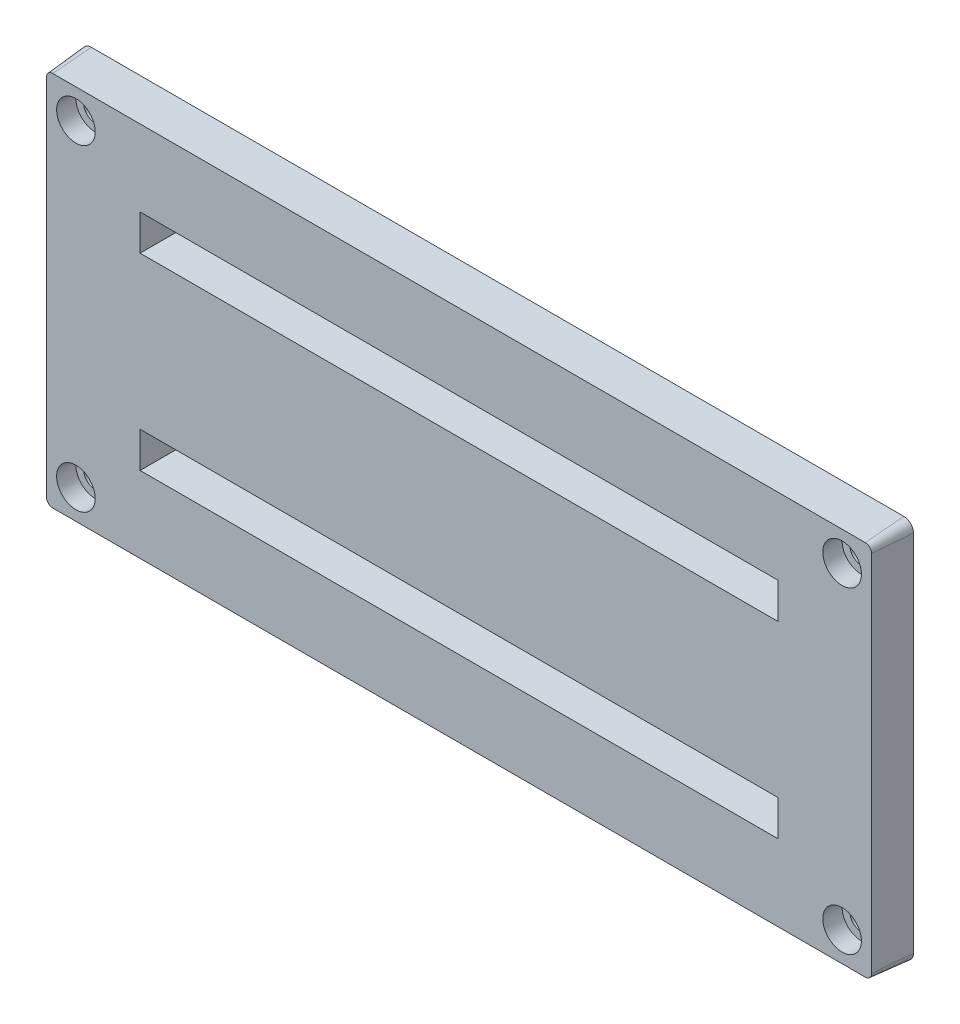
SolidWorks part; units mm, degrees
ref_plane "Спереди" through (0, 0, 0) normal (0, 0, 1) x (1, 0, 0)
ref_plane "Сверху" through (0, 0, 0) normal (0, 1, 0) x (1, 0, 0)
ref_plane "Справа" through (0, 0, 0) normal (1, 0, 0) x (0, 0, -1)
sketch "Sketch1" plane through (0, 0, 11.6) normal (0, 0, 1) x (1, 0, 0)
  line L0 (-42.1, -10.1) -> (42.1, -10.1) construction
  line L1 (-43.1, 28.6) -> (-43.1, -9.1) construction
  line L2 (43.1, -9.1) -> (43.1, 28.6) construction
  line L3 (42.1, 29.6) -> (-42.1, 29.6) construction
  line L4 (-42.1, -10.1) -> (42.1, -10.1)
  line L5 (-43.1, 28.6) -> (-43.1, -9.1)
  line L6 (43.1, -9.1) -> (43.1, 28.6)
  line L7 (42.1, 29.6) -> (-42.1, 29.6)
  line L12 (-32.7, 1.5) -> (-32.7, -1.5) construction
  line L13 (-32.7, -1.5) -> (32.7, -1.5) construction
  line L14 (32.7, -1.5) -> (32.7, 1.5) construction
  line L15 (32.7, 1.5) -> (-32.7, 1.5) construction
  line L16 (32.7, 18) -> (32.7, 21) construction
  line L17 (-32.7, 18) -> (32.7, 18) construction
  line L18 (-32.7, 21) -> (-32.7, 18) construction
  line L19 (32.7, 21) -> (-32.7, 21) construction
  line L20 (-32.7, 1.5) -> (-32.7, -1.5)
  line L21 (-32.7, -1.5) -> (32.7, -1.5)
  line L22 (32.7, -1.5) -> (32.7, 1.5)
  line L23 (32.7, 1.5) -> (-32.7, 1.5)
  line L24 (32.7, 18) -> (32.7, 21)
  line L25 (-32.7, 18) -> (32.7, 18)
  line L26 (-32.7, 21) -> (-32.7, 18)
  line L27 (32.7, 21) -> (-32.7, 21)
  arc A0 (-43.1, -9.1) -> (-42.1, -10.1) centre (-42.1, -9.1) ccw construction
  arc A1 (42.1, -10.1) -> (43.1, -9.1) centre (42.1, -9.1) ccw construction
  arc A2 (-42.1, 29.6) -> (-43.1, 28.6) centre (-42.1, 28.6) ccw construction
  arc A3 (43.1, 28.6) -> (42.1, 29.6) centre (42.1, 28.6) ccw construction
  arc A4 (-43.1, -9.1) -> (-42.1, -10.1) centre (-42.1, -9.1) ccw
  arc A5 (42.1, -10.1) -> (43.1, -9.1) centre (42.1, -9.1) ccw
  arc A6 (-42.1, 29.6) -> (-43.1, 28.6) centre (-42.1, 28.6) ccw
  arc A7 (43.1, 28.6) -> (42.1, 29.6) centre (42.1, 28.6) ccw
extrude "Boss-Extrude1" add sketch "Sketch1" along normal blind 4 draft 5
sketch "Sketch2" plane through (0, 0, 15.6) normal (0, 0, 1) x (1, 0, 0)
  circle A0 centre (-39.7, 26.2) radius 1.2
  circle A1 centre (-39.7, -6.7) radius 1.2
  circle A2 centre (39.7, -6.7) radius 1.2
  circle A3 centre (39.7, 26.2) radius 1.2
  dimension "D1" = 2.4
extrude "Cut-Extrude1" cut sketch "Sketch2" against normal through all
sketch "Sketch3" plane through (0, 0, 15.6) normal (0, 0, 1) x (1, 0, 0)
  circle A0 centre (-39.7, 26.2) radius 2
  circle A1 centre (-39.7, -6.7) radius 2
  circle A2 centre (39.7, -6.7) radius 2
  circle A3 centre (39.7, 26.2) radius 2
  dimension "D1" = 4
extrude "Cut-Extrude2" cut sketch "Sketch3" against normal blind 2
